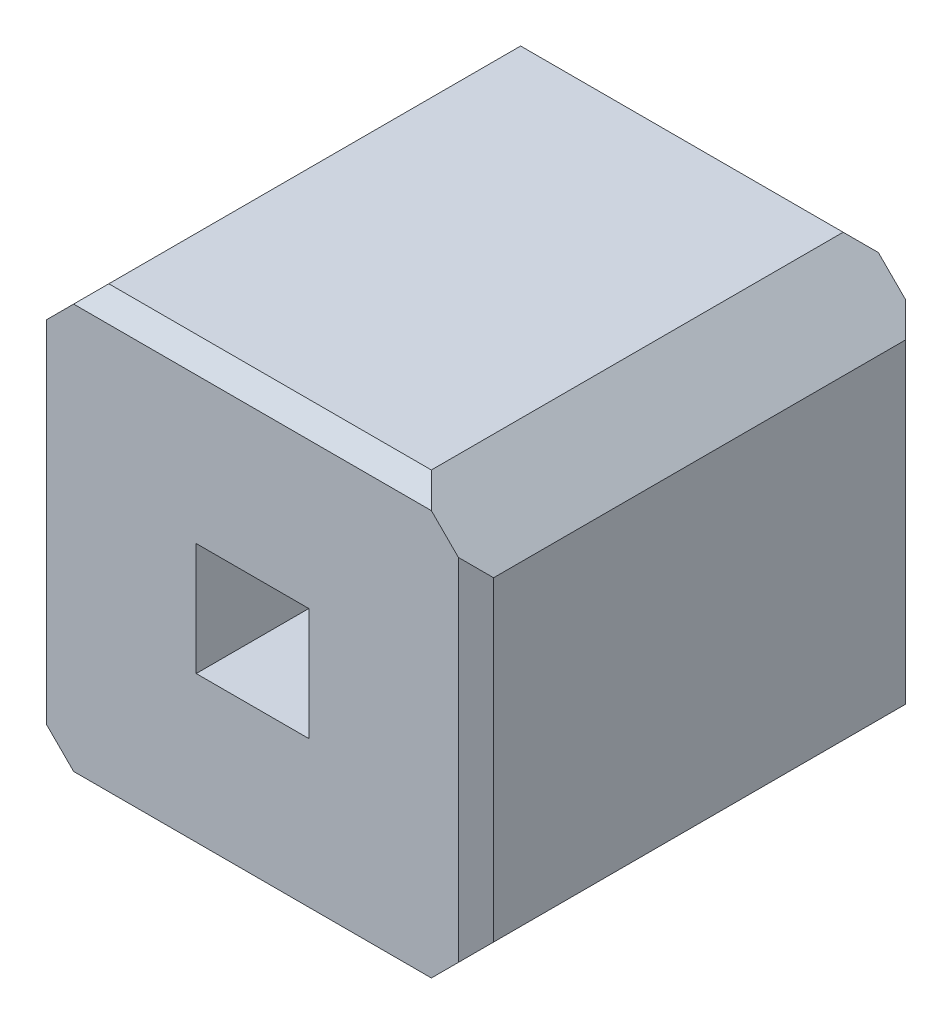
SolidWorks part; units mm, degrees
ref_plane "Спереди" through (0, 0, 0) normal (0, 0, 1) x (1, 0, 0)
ref_plane "Сверху" through (0, 0, 0) normal (0, 1, 0) x (1, 0, 0)
ref_plane "Справа" through (0, 0, 0) normal (1, 0, 0) x (0, 0, -1)
sketch "Model" plane through (0, 0, 0) normal (0, 0, 1) x (1, 0, 0)
  line L0 (-2.3258, -0.2142) -> (-2.3258, 0.2142) construction
  line L1 (-2.22, 0.32) -> (-2.3258, 0.2142) construction
  line L2 (-2.22, 0.32) -> (-2.22, -0.32)
  line L3 (-2.3258, -0.2142) -> (-2.22, -0.32) construction
  line L4 (-2.7542, 0.2142) -> (-2.7542, -0.2142) construction
  line L5 (-2.3258, 0.2142) -> (-2.7542, 0.2142) construction
  line L6 (-2.7542, -0.2142) -> (-2.3258, -0.2142) construction
  line L7 (-2.86, 0.32) -> (-2.22, 0.32)
  line L8 (-2.86, 0.32) -> (-2.7542, 0.2142) construction
  line L9 (-2.22, -0.32) -> (-2.86, -0.32)
  line L10 (-2.7542, -0.2142) -> (-2.86, -0.32) construction
  line L11 (-2.86, -0.32) -> (-2.86, 0.32)
  line L12 (-1.27, -0.8964) -> (-1.27, 0.8964)
  line L13 (-1.37, -0.9964) -> (-1.37, 0.9964) construction
  line L14 (-1.6236, -1.25) -> (-1.27, -0.8964)
  line L15 (-1.27, 0.8964) -> (-1.6236, 1.25)
  line L16 (-3.4564, -1.25) -> (-1.6236, -1.25)
  line L17 (-3.81, -0.8964) -> (-3.4564, -1.25)
  line L18 (-3.71, 0.9964) -> (-3.71, -0.9964) construction
  line L19 (-3.4564, 1.25) -> (-3.81, 0.8964)
  line L20 (-1.6236, 1.25) -> (-3.4564, 1.25)
  line L21 (-3.81, -0.8964) -> (-3.81, 0.8964)
extrude "Бобышка-Вытянуть1" add sketch "Model" along normal blind 2.54
chamfer "Фаска1" distance 0.1 angle 45 8 edges at (-1.27, 0, 0) (-3.81, 0, 2.54) (-3.81, 0, 0) (-1.27, 0, 2.54) (-2.54, -1.25, 2.54) (-2.54, 1.25, 0) (-2.54, -1.25, 0) (-2.54, 1.25, 2.54)
